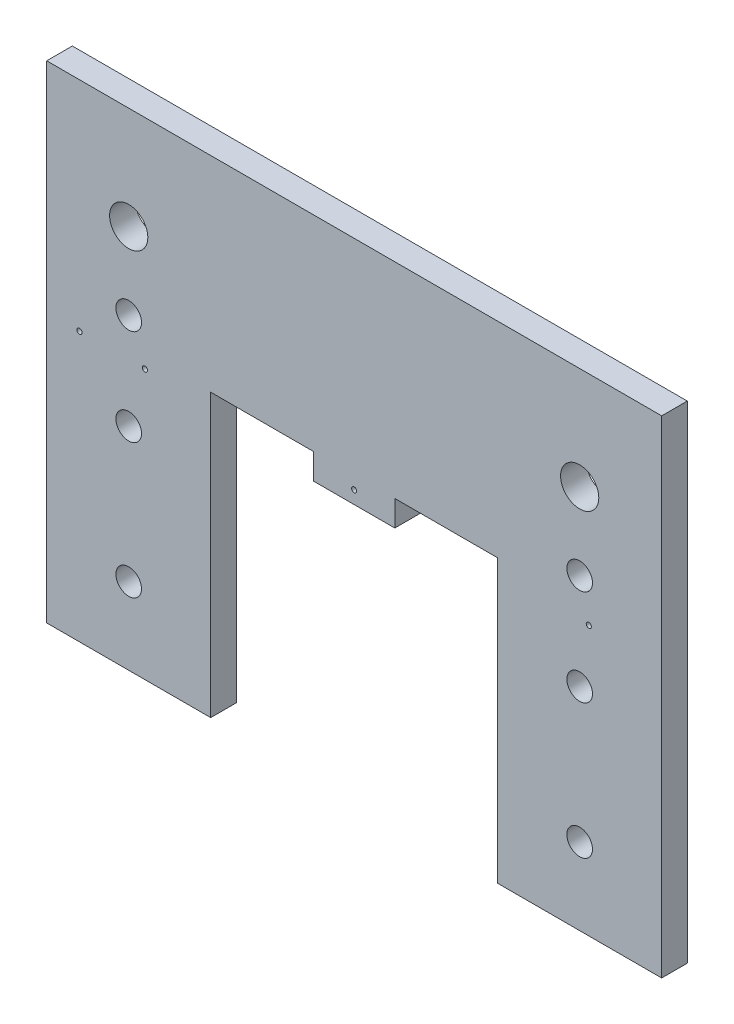
SolidWorks part; units mm, degrees
ref_plane "Front Plane" through (0, 0, 0) normal (0, 0, 1) x (1, 0, 0)
ref_plane "Top Plane" through (0, 0, 0) normal (0, 1, 0) x (1, 0, 0)
ref_plane "Right Plane" through (0, 0, 0) normal (1, 0, 0) x (0, 0, -1)
sketch "Sketch1" plane through (0, 0, 0) normal (0, 0, 1) x (1, 0, 0)
  line L0 (0, 69.85) -> (40.64, 69.85) construction
  line L1 (0, 0) -> (40.64, 0)
  line L2 (0, 69.85) -> (0, 120.65)
  line L3 (0, 120.65) -> (40.64, 120.65)
  line L4 (152.4, 69.85) -> (152.4, 120.65)
  line L5 (40.64, 120.65) -> (40.64, 69.85) construction
  line L6 (111.76, 120.65) -> (111.76, 69.85) construction
  line L7 (111.76, 120.65) -> (152.4, 120.65)
  line L8 (40.64, 120.65) -> (111.76, 120.65)
  line L9 (0, 69.85) -> (0, 0)
  line L10 (152.4, 69.85) -> (152.4, 0)
  line L11 (0, 95.25) -> (40.64, 95.25) construction
  line L12 (111.76, 95.25) -> (152.4, 95.25) construction
  line L13 (111.76, 0) -> (152.4, 0)
  line L14 (111.76, 69.85) -> (152.4, 69.85) construction
  line L15 (40.64, 0) -> (40.64, 63.5)
  line L16 (40.64, 69.85) -> (111.76, 69.85) construction
  line L17 (111.76, 63.5) -> (111.76, 0)
  line L18 (20.32, 120.65) -> (20.32, 0) construction
  line L19 (132.08, 120.65) -> (132.08, 0) construction
  line L20 (40.64, 63.5) -> (111.76, 63.5)
  circle A0 centre (20.32, 95.25) radius 4.7371
  circle A1 centre (132.08, 95.25) radius 4.7371
  circle A2 centre (132.08, 76.2) radius 3.175
  circle A3 centre (20.32, 76.2) radius 3.175
  circle A4 centre (20.32, 52.3875) radius 3.175
  circle A5 centre (132.08, 52.3875) radius 3.175
  circle A6 centre (20.32, 19.05) radius 3.175
  circle A7 centre (132.08, 19.05) radius 3.175
  dimension "D5" = 9.4742
  dimension "D6" = 19.05
  dimension "D7" = 6.35
  dimension "D9" = 23.8125
  dimension "D1" = 152.4
  dimension "D2" = 50.8
  dimension "D3" = 40.64
  dimension "D4" = 120.65
  dimension "D8" = 19.05
  dimension "D10" = 23.8125
  dimension "D11" = 33.3375
  dimension "D12" = 33.3375
  dimension "D13" = 57.15
extrude "Boss-Extrude1" add sketch "Sketch1" along normal blind 6.35
sketch "Sketch2" plane through (0, 0, 0) normal (0, 0, -1) x (-1, 0, 0)
  line L0 (-152.4, 69.85) -> (-111.76, 69.85) construction
  line L1 (-111.76, 63.5) -> (-86.2617, 63.5)
  line L2 (-111.76, 63.5) -> (-111.76, 69.85)
  line L3 (-111.76, 69.85) -> (-86.2617, 69.85)
  line L4 (-86.2617, 63.5) -> (-86.2617, 69.85)
  line L5 (-40.64, 63.5) -> (-66.1383, 63.5)
  line L6 (-40.64, 63.5) -> (-40.64, 69.85)
  line L7 (-40.64, 69.85) -> (-66.1383, 69.85)
  line L8 (-66.1383, 63.5) -> (-66.1383, 69.85)
  line L9 (-66.1383, 63.5) -> (-66.1383, 69.85) construction
extrude "Cut-Extrude1" cut sketch "Sketch2" against normal blind 6.35
sketch "Sketch3" plane through (0, 0, 0) normal (0, 0, -1) x (-1, 0, 0)
  line L0 (-152.4, 69.85) -> (-116.2799, 69.85) construction
  line L1 (-86.2617, 69.85) -> (-66.1383, 69.85) construction
  line L2 (-86.2617, 69.85) -> (-86.2617, 63.5) construction
  line L3 (-86.2617, 63.5) -> (-66.1383, 63.5) construction
  line L4 (-111.76, 63.5) -> (-111.76, 69.85)
  line L5 (-111.76, 69.85) -> (-152.4, 69.85)
  line L6 (-152.4, 69.85) -> (-152.4, 63.5)
  line L7 (-152.4, 63.5) -> (-111.76, 63.5)
  line L8 (-111.76, 63.5) -> (-111.76, 69.85) construction
  line L9 (-116.2799, 69.85) -> (-152.4, 69.85) construction
  line L10 (-152.4, 69.85) -> (-152.4, 63.5) construction
  line L11 (-152.4, 63.5) -> (-111.76, 63.5) construction
  line L12 (-40.64, 69.85) -> (-40.64, 63.5)
  line L13 (-40.64, 63.5) -> (0, 63.5)
  line L14 (0, 63.5) -> (0, 69.85)
  line L15 (0, 69.85) -> (-40.64, 69.85)
  line L16 (-40.64, 69.85) -> (-40.64, 63.5) construction
  line L17 (-40.64, 63.5) -> (0, 63.5) construction
  line L18 (0, 63.5) -> (0, 69.85) construction
  line L19 (-24.3422, 69.85) -> (-24.3422, 66.675) construction
  line L20 (-66.1383, 69.85) -> (-66.1383, 63.5) construction
  line L21 (-116.2799, 69.85) -> (-80.1597, 69.85) construction
  line L22 (-32.4562, 69.85) -> (-16.2281, 69.85) construction
  line L23 (-16.2281, 69.85) -> (0, 69.85) construction
  line L24 (-152.4, 66.675) -> (-134.3399, 66.675) construction
  line L25 (-134.3399, 66.675) -> (-134.3399, 69.85) construction
  line L26 (-134.3399, 69.85) -> (-98.2198, 66.675) construction
  line L27 (-98.2198, 66.675) -> (-111.76, 66.675) construction
  line L28 (-80.1597, 69.85) -> (-98.2198, 69.85) construction
  line L29 (-98.2198, 69.85) -> (-98.2198, 66.675) construction
  line L30 (-76.2, 69.85) -> (-76.2, 66.675) construction
  line L31 (-76.2, 66.675) -> (-86.2617, 66.675) construction
  line L32 (-24.3422, 66.675) -> (-40.64, 66.675) construction
  line L33 (-40.64, 66.675) -> (-8.1141, 66.675) construction
  line L34 (-8.1141, 66.675) -> (-8.1141, 69.85) construction
  circle A0 centre (-134.3399, 66.675) radius 0.635
  circle A1 centre (-98.2198, 66.675) radius 0.635
  circle A2 centre (-24.3422, 66.675) radius 0.635
  circle A3 centre (-76.2, 66.675) radius 0.635
  circle A4 centre (-8.1141, 66.675) radius 0.635
  dimension "D1" = 0
  dimension "D2" = 0
extrude "Cut-Extrude2" cut sketch "Sketch3" against normal blind 6.35
